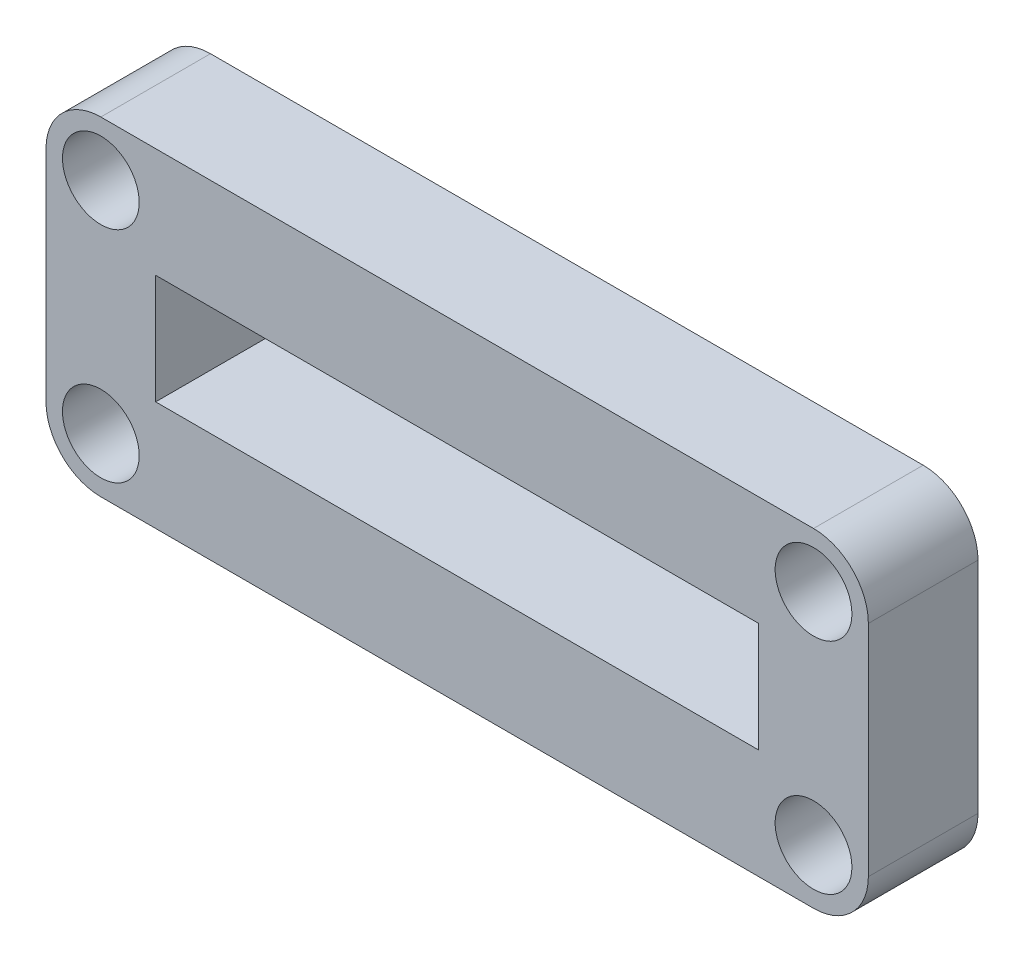
SolidWorks part; units mm, degrees
ref_plane "Front" through (0, 0, 0) normal (0, 0, 1) x (1, 0, 0)
ref_plane "Top" through (0, 0, 0) normal (0, 1, 0) x (1, 0, 0)
ref_plane "Right" through (0, 0, 0) normal (1, 0, 0) x (0, 0, -1)
sketch "Sketch1" plane through (0, 0, 0) normal (0, 0, 1) x (1, 0, 0)
  line L0 (-3, 0) -> (-3, -8)
  line L1 (0, -11) -> (26, -11)
  line L2 (29, 0) -> (29, -8)
  line L3 (0, 3) -> (26, 3)
  line L4 (23, -3) -> (3, -3)
  line L5 (3, -5) -> (3, -3)
  line L7 (23, -3) -> (23, -5)
  line L8 (23, -5) -> (3, -5)
  circle A0 centre (0, 0) radius 1.4
  circle A1 centre (0, -8) radius 1.4
  circle A2 centre (26, 0) radius 1.4
  circle A3 centre (26, -8) radius 1.4
  arc A4 (0, 3) -> (-3, 0) centre (0, 0) ccw
  arc A5 (-3, -8) -> (0, -11) centre (0, -8) ccw
  arc A6 (29, 0) -> (26, 3) centre (26, 0) ccw
  arc A7 (26, -11) -> (29, -8) centre (26, -8) ccw
extrude "Boss-Extrude1" add sketch "Sketch1" along normal blind 7
sketch "Sketch2" plane through (0, 0, 7) normal (0, 0, 1) x (1, 0, 0)
  line L0 (-2, 0) -> (-2, -8)
  line L1 (0, -10) -> (26, -10)
  line L2 (28, -8) -> (28, 0)
  line L3 (26, 2) -> (0, 2)
  line L4 (2, 0) -> (2, -8)
  line L5 (0, -2) -> (26, -2)
  line L6 (24, 0) -> (24, -8)
  line L7 (0, -6) -> (26, -6)
  circle A0 centre (0, 0) radius 2
  circle A1 centre (26, 0) radius 2
  circle A2 centre (26, -8) radius 2
  circle A3 centre (0, -8) radius 2
  arc M5 (0, 3) -> (-3, 0) centre (0, 0) ccw
  line M6 (-3, 0) -> (-3, -8)
  arc M7 (-3, -8) -> (0, -11) centre (0, -8) ccw
  line M8 (0, -11) -> (26, -11)
  arc M9 (26, -11) -> (29, -8) centre (26, -8) ccw
  line M10 (29, -8) -> (29, 0)
  arc M11 (29, 0) -> (26, 3) centre (26, 0) ccw
  line M12 (26, 3) -> (0, 3)
  line M15 (3, -3) -> (23, -3)
  line M16 (23, -3) -> (23, -5)
  line M17 (23, -5) -> (3, -5)
  line M18 (3, -5) -> (3, -3)
extrude "Cut-Extrude1" cut sketch "Sketch2" against normal blind 8.5 contours L4 L7 L6 L5 M18 M15 M16 M17 | A3 L0 A0 L3 A1 L2 A2 L1 M12 M5 M6 M7 M8 M9 M10 M11
sketch "Sketch3" plane through (0, 0, 7) normal (0, 0, 1) x (1, 0, 0)
  circle A0 centre (0, 0.2788) radius 39.7989
extrude "Cut-Extrude2" cut sketch "Sketch3" against normal blind 3
